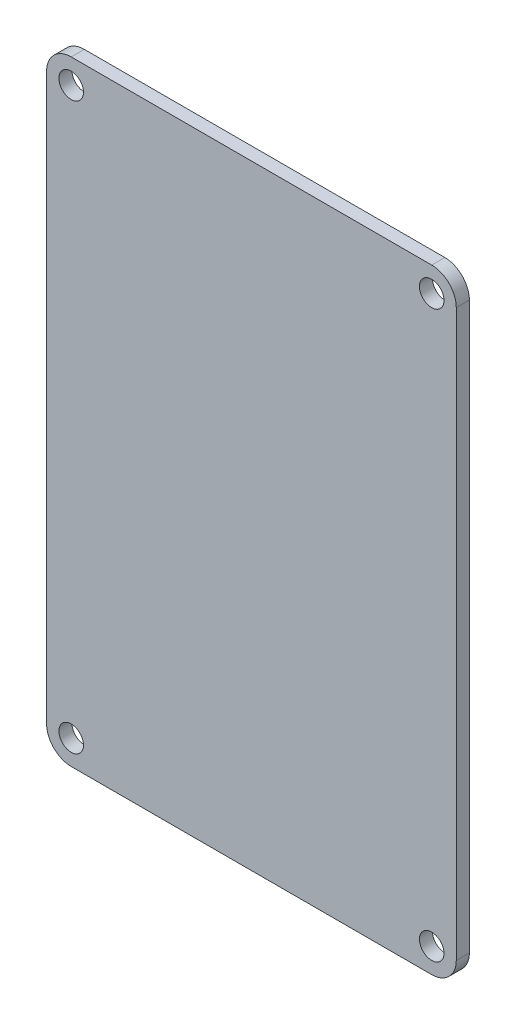
SolidWorks part; units mm, degrees
ref_plane "Front Plane" through (0, 0, 0) normal (0, 0, 1) x (1, 0, 0)
ref_plane "Top Plane" through (0, 0, 0) normal (0, 1, 0) x (1, 0, 0)
ref_plane "Right Plane" through (0, 0, 0) normal (1, 0, 0) x (0, 0, -1)
sketch "Sketch1" plane through (0, 0, 0) normal (0, 0, 1) x (1, 0, 0)
  line L1 (-22, -37.5) -> (22, -37.5)
  line L2 (-25, -34.5) -> (-25, 34.5)
  line L3 (-22, 37.5) -> (22, 37.5)
  line L4 (25, -34.5) -> (25, 34.5)
  line L5 (-25, -37.5) -> (25, 37.5) construction
  line L6 (-25, 37.5) -> (25, -37.5) construction
  arc A0 (25, 34.5) -> (22, 37.5) centre (22, 34.5) ccw
  arc A1 (25, -34.5) -> (22, -37.5) centre (22, -34.5) cw
  arc A2 (-22, -37.5) -> (-25, -34.5) centre (-22, -34.5) cw
  arc A3 (-25, 34.5) -> (-22, 37.5) centre (-22, 34.5) cw
  point P0 (0, 0)
  dimension "D3" = 3
  dimension "D1" = 50
  dimension "D2" = 75
extrude "Boss-Extrude1" add sketch "Sketch1" along normal blind 1.6
sketch "Sketch2" plane through (0, 0, 0) normal (0, 0, -1) x (-1, 0, 0)
  circle A12 centre (-22, 34.5) radius 1.5
  circle A13 centre (22, 34.5) radius 1.5
  circle A14 centre (22, -34.5) radius 1.5
  circle A15 centre (-22, -34.5) radius 1.5
extrude "Cut-Extrude1" cut sketch "Sketch2" against normal through all
